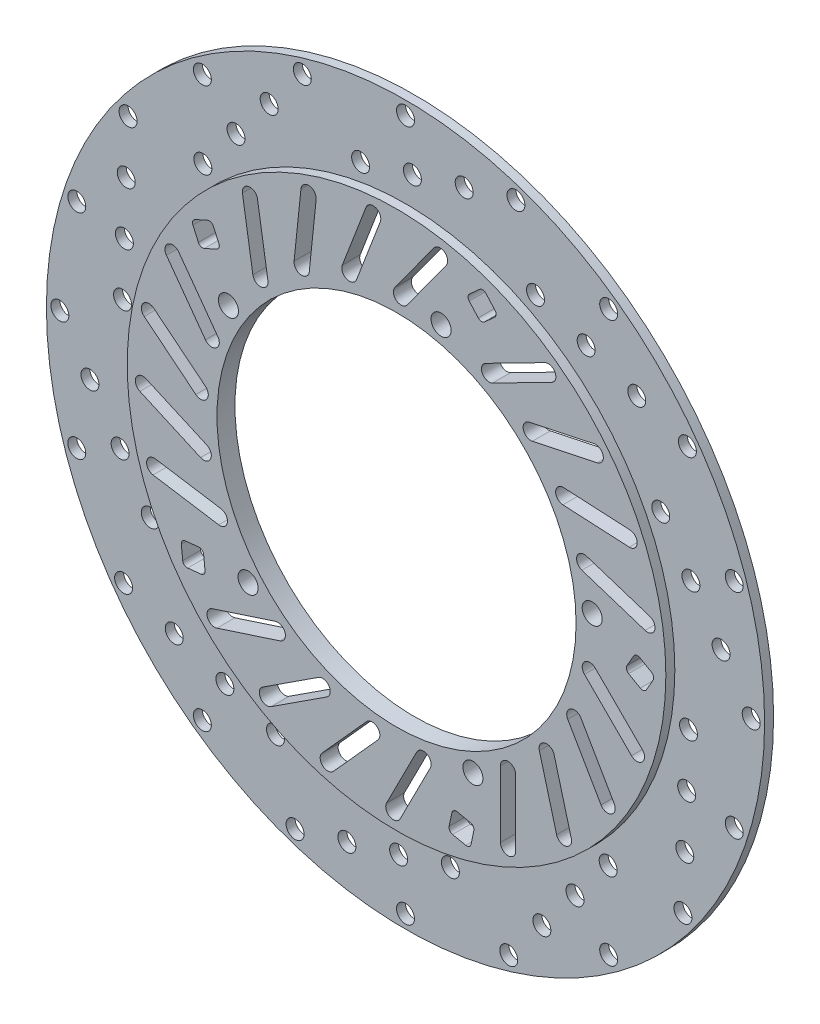
SolidWorks part; units mm, degrees
ref_plane "Front Plane" through (0, 0, 0) normal (0, 0, 1) x (1, 0, 0)
ref_plane "Top Plane" through (0, 0, 0) normal (0, 1, 0) x (1, 0, 0)
ref_plane "Right Plane" through (0, 0, 0) normal (1, 0, 0) x (0, 0, -1)
sketch "Sketch1" plane through (0, 0, 0) normal (0, 0, 1) x (1, 0, 0)
  circle A0 centre (0, 0) radius 300
  circle A1 centre (0, 0) radius 200
  dimension "D1" = 600
  dimension "D2" = 400
extrude "Boss-Extrude1" add sketch "Sketch1" along normal blind 20
sketch "Sketch2" plane through (0, 0, 0) normal (0, 0, 1) x (1, 0, 0)
  circle A0 centre (0, 0) radius 400
  circle A1 centre (0, 0) radius 300 construction
  circle A2 centre (0, 0) radius 300
  dimension "D1" = 800
extrude "Boss-Extrude3" add sketch "Sketch2" along normal blind 10 contours A0 | A2
sketch "Sketch3" plane through (0, 0, 0) normal (0, 0, 1) x (1, 0, 0)
  circle A2 centre (0, 385) radius 10
  circle A4 centre (-50, 315.2057) radius 10
  circle A5 centre (123.0063, 364.893) radius 10
  circle A6 centre (7.6688, 331.7681) radius 10
  circle A7 centre (65.3375, 348.3306) radius 10
  dimension "D2" = 20
  dimension "D4" = 20
  dimension "D7" = 20
  dimension "D8" = 60
  dimension "D10" = 20
  dimension "D5" = 180
  dimension "D6" = 60
extrude "Cut-Extrude3" cut sketch "Sketch3" along normal blind 44
pattern_circular "CirPattern1" count 10 over 360 about axis through (0, 0, 0) along (0, 0, 1) of "Cut-Extrude3"
ref_plane "Plane1" through (0, 0, 20) normal (0, 0, 1) x (1, 0, 0)
sketch "Sketch4" plane through (0, 0, 20) normal (0, 0, 1) x (1, 0, 0)
  line L1 (-200.3878, 160.8295) -> (-214.087, 154.7196)
  line L2 (48.4641, 278.0551) -> (5.0068, 218.1596) construction
  line L3 (55.3439, 273.0633) -> (11.8866, 213.1679)
  line L4 (41.5842, 283.0468) -> (-1.8731, 223.1513)
  line L5 (-220.6901, 157.2494) -> (-226.8, 170.9486)
  line L6 (-224.2702, 177.5516) -> (-210.571, 183.6616)
  line L7 (-26.0314, 281.4477) -> (-52.5059, 212.3456) construction
  line L8 (-18.094, 278.4068) -> (-44.5685, 209.3046)
  line L9 (-33.9688, 284.4887) -> (-60.4433, 215.3866)
  line L10 (-203.9679, 181.1318) -> (-197.858, 167.4326)
  line L12 (-97.9885, 265.1202) -> (-105.6759, 191.5206) construction
  line L13 (-89.5345, 264.2372) -> (-97.2219, 190.6376)
  line L14 (-106.4425, 266.0032) -> (-114.1299, 192.4036)
  line L17 (-163.2678, 230.7252) -> (-151.6442, 157.6438) construction
  line L18 (-154.8733, 232.0603) -> (-143.2497, 158.9789)
  line L19 (-171.6622, 229.3901) -> (-160.0387, 156.3086)
  arc A1 (55.3439, 273.0633) -> (41.5842, 283.0468) centre (48.4641, 278.0551) ccw
  arc A2 (-1.8731, 223.1513) -> (11.8866, 213.1679) centre (5.0068, 218.1596) ccw
  arc A3 (-18.094, 278.4068) -> (-33.9688, 284.4887) centre (-26.0314, 281.4477) ccw
  arc A4 (-60.4433, 215.3866) -> (-44.5685, 209.3046) centre (-52.5059, 212.3456) ccw
  arc A5 (-89.5345, 264.2372) -> (-106.4425, 266.0032) centre (-97.9885, 265.1202) ccw
  arc A6 (-114.1299, 192.4036) -> (-97.2219, 190.6376) centre (-105.6759, 191.5206) ccw
  arc A7 (-154.8733, 232.0603) -> (-171.6622, 229.3901) centre (-163.2678, 230.7252) ccw
  arc A8 (-160.0387, 156.3086) -> (-143.2497, 158.9789) centre (-151.6442, 157.6438) ccw
  circle A9 centre (-187.2783, 113.0238) radius 11.175
  arc A10 (-197.858, 167.4326) -> (-200.3878, 160.8295) centre (-202.4244, 165.3959) cw
  arc A11 (-214.087, 154.7196) -> (-220.6901, 157.2494) centre (-216.1236, 159.286) cw
  arc A12 (-210.571, 183.6616) -> (-203.9679, 181.1318) centre (-208.5344, 179.0952) cw
  arc A13 (-226.8, 170.9486) -> (-224.2702, 177.5516) centre (-222.2336, 172.9852) cw
  point P6 (26.7354, 248.1073)
  point P11 (-39.2687, 246.8967)
  point P15 (-39.2687, 246.8967)
  point P23 (-101.8322, 228.3204)
  point P28 (-157.456, 194.1845)
  point P32 (-157.456, 194.1845)
  point P37 (-195.8214, 162.8662)
  point P40 (-202.3494, 146.8152)
  point P47 (-206.0046, 185.6982)
  point P50 (-228.8366, 175.515)
  dimension "D21" = 22.35
  dimension "D3" = 5
  dimension "D2" = 74
  dimension "D5" = 25
  dimension "D6" = 25
  dimension "D8" = 17
  dimension "D9" = 17
  dimension "D11" = 74
  dimension "D17" = 17
  dimension "D18" = 17
extrude "Cut-Extrude4" cut sketch "Sketch4" against normal blind 44
pattern_circular "CirPattern2" count 5 over 360 about axis through (0, 0, 0) along (0, 0, 1) of "Cut-Extrude4"
